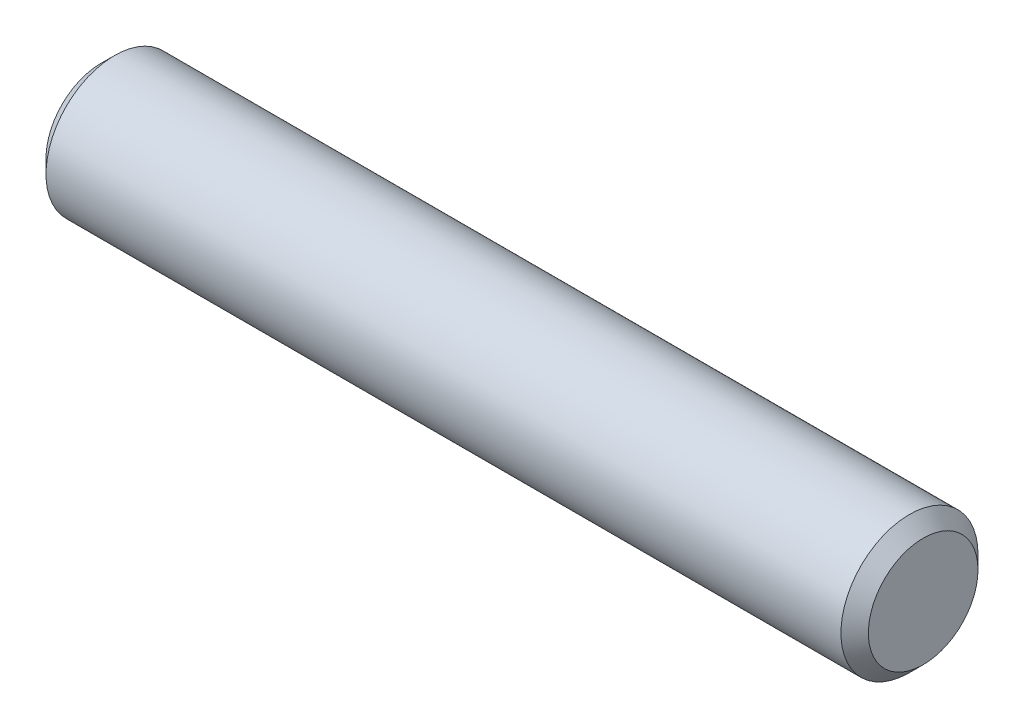
SolidWorks part; units mm, degrees
material "AISI 304"
ref_plane "Front" through (0, 0, 0) normal (0, 0, 1) x (1, 0, 0)
ref_plane "Top" through (0, 0, 0) normal (0, 1, 0) x (1, 0, 0)
ref_plane "Right" through (0, 0, 0) normal (1, 0, 0) x (0, 0, -1)
sketch "Sketch1" plane through (0, 0, 0) normal (0, 0, 1) x (1, 0, 0)
  line L0 (-4.7625, 0) -> (4.7625, 0) construction
  line L1 (4.7625, 0.7937) -> (4.7625, -0.7937) construction
  line L2 (-4.7625, 0.7937) -> (-4.7625, -0.7937) construction
  dimension "Length" = 9.525
  dimension "Diameter" = 1.5875
sketch "Sketch2" plane through (0, 0, 0) normal (1, 0, 0) x (0, 0, -1)
  circle A0 centre (0, 0) radius 0.7937
extrude "Extrude1" add sketch "Sketch2" against normal up to vertex (4.7625 mm away) and the other way up to vertex (4.7625 mm away) up to point (-4.7625, 0.7937, 0) other way up to point (4.7625, 0.7937, 0)
chamfer "Chamfer1" distance 0.1588 angle 45 2 edges at (4.7625, 0, -0.7937) (-4.7625, 0, -0.7937)
equation "\"D1@Chamfer1\" = \"Diameter@Sketch1\"*.1"
